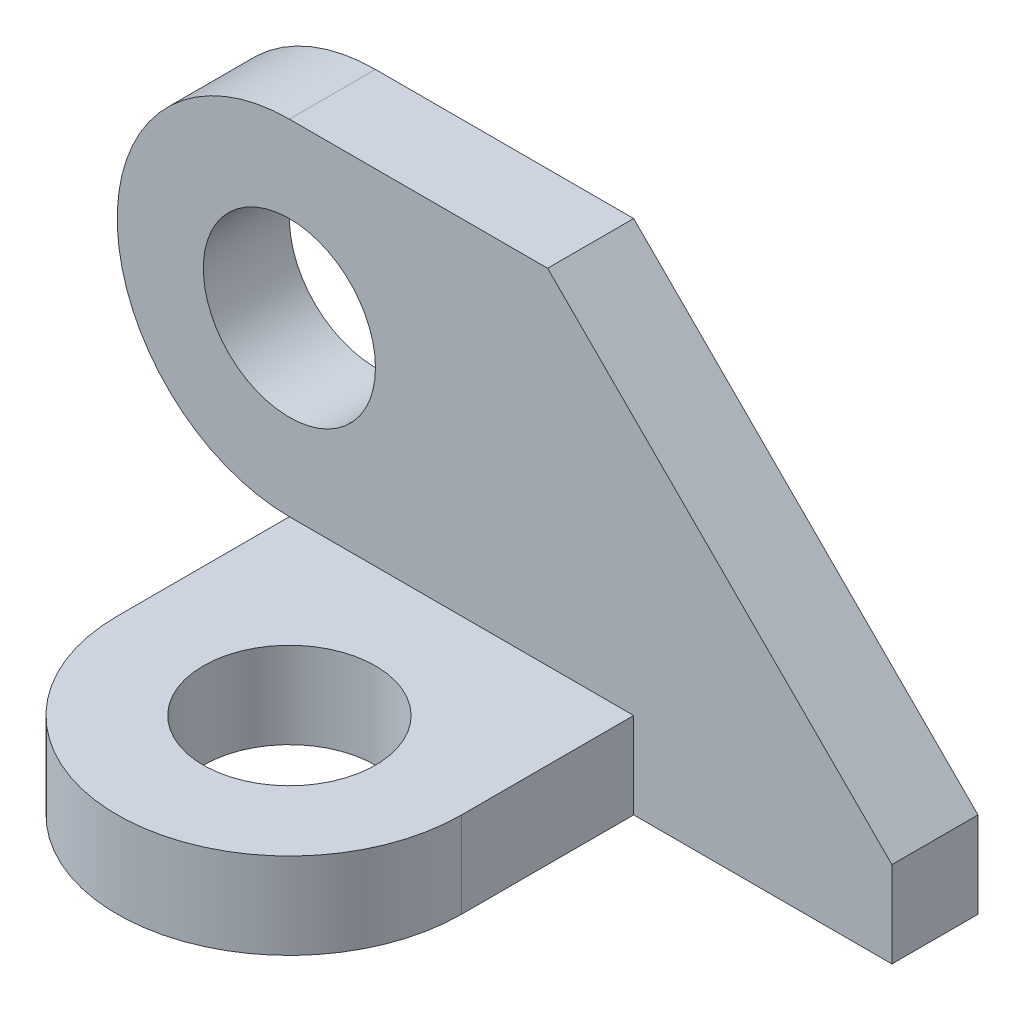
SolidWorks part; units mm, degrees
ref_plane "前基準面" through (0, 0, 0) normal (0, 0, 1) x (1, 0, 0)
ref_plane "上基準面" through (0, 0, 0) normal (0, 1, 0) x (1, 0, 0)
ref_plane "右基準面" through (0, 0, 0) normal (1, 0, 0) x (0, 0, -1)
sketch "草圖1" plane through (0, 0, 0) normal (0, 0, 1) x (1, 0, 0)
  line L0 (0, 10) -> (15, 10)
  line L1 (15, 10) -> (35, -10)
  line L2 (35, -10) -> (35, -15)
  line L3 (35, -15) -> (0, -15)
  line L4 (0, -15) -> (0, -10)
  circle A0 centre (0, 0) radius 5
  arc A1 (0, 10) -> (0, -10) centre (0, 0) ccw
  dimension "D1" = 10
  dimension "D2" = 20
  dimension "D3" = 15
  dimension "D4" = 5
  dimension "D5" = 35
  dimension "D6" = 5
extrude "填料-伸長1" add sketch "草圖1" along normal blind 5
sketch "草圖2" plane through (0, 0, 0) normal (0, 1, 0) x (1, 0, 0)
  line L0 (0, 0) -> (0, -15) construction
  line L1 (0, -15) -> (10, -15) construction
  line L2 (10, -15) -> (10, -12.0355) construction
  line L3 (0, -15) -> (0, -5)
  line L4 (20, -15) -> (20, -5)
  line L5 (35, -5) -> (15, -5) construction
  line L6 (20, -5) -> (0, -5)
  circle A0 centre (10, -15) radius 5
  arc A1 (0, -15) -> (20, -15) centre (10, -15) ccw
  dimension "D3" = 20
  dimension "D4" = 10
  dimension "D2" = 15
extrude "填料-伸長2" add sketch "草圖2" along normal blind 5 from surface at -15 starting at face at (17.5, -15, 2.5)
scale "縮放比例1" scale about centroid uniform scaling yes scale factor 0.2
